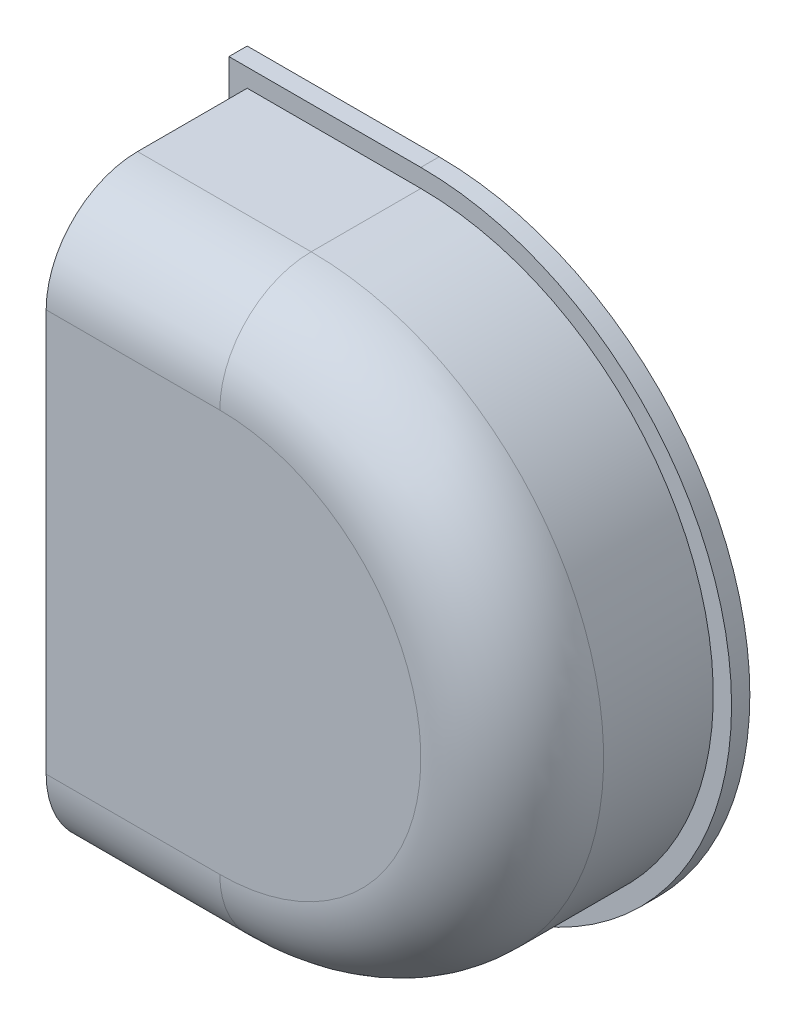
SolidWorks part; units mm, degrees
ref_plane "Front Plane" through (0, 0, 0) normal (0, 0, 1) x (1, 0, 0)
ref_plane "Top Plane" through (0, 0, 0) normal (0, 1, 0) x (1, 0, 0)
ref_plane "Right Plane" through (0, 0, 0) normal (1, 0, 0) x (0, 0, -1)
sketch "Sketch2" plane through (0, 0, 0) normal (0, 0, 1) x (1, 0, 0)
  line L0 (0, 0) -> (0, 64)
  line L1 (0, 64) -> (19, 64)
  line L2 (19, 0) -> (0, 0)
  arc A0 (19, 64) -> (19, 0) centre (19, 32) cw
  dimension "D1" = 19
  dimension "D2" = 64
extrude "Boss-Extrude3" add sketch "Sketch2" along normal blind 22
fillet "Fillet2" radius 10 3 edges at (9.5, 0, 22) (51, 32, 22) (9.5, 64, 22)
shell "Shell1" thickness 3
sketch "Sketch3" plane through (0, 0, 0) normal (0, 0, -1) x (-1, 0, 0)
  line L0 (-3, 3) -> (-3, 61)
  line L1 (-3, 61) -> (-19, 61)
  line L2 (-19, 3) -> (-3, 3)
  line L9 (2, -2) -> (2, 66)
  line L10 (2, 66) -> (-19, 66)
  line L11 (-19, -2) -> (2, -2)
  arc A0 (-19, 61) -> (-19, 3) centre (-19, 32) ccw
  arc A3 (-19, 66) -> (-19, -2) centre (-19, 32) ccw
extrude "Boss-Extrude4" add sketch "Sketch3" along normal blind 2
sketch "Sketch4" plane through (0, 0, 19) normal (0, 0, -1) x (-1, 0, 0)
  line L0 (-19, 10) -> (-19, 54) construction
  circle A0 centre (-19, 32) radius 5
  dimension "D1" = 10
extrude "Boss-Extrude5" add sketch "Sketch4" along normal offset from surface (11 mm away) 10 up to face at (17, 32, -2)
